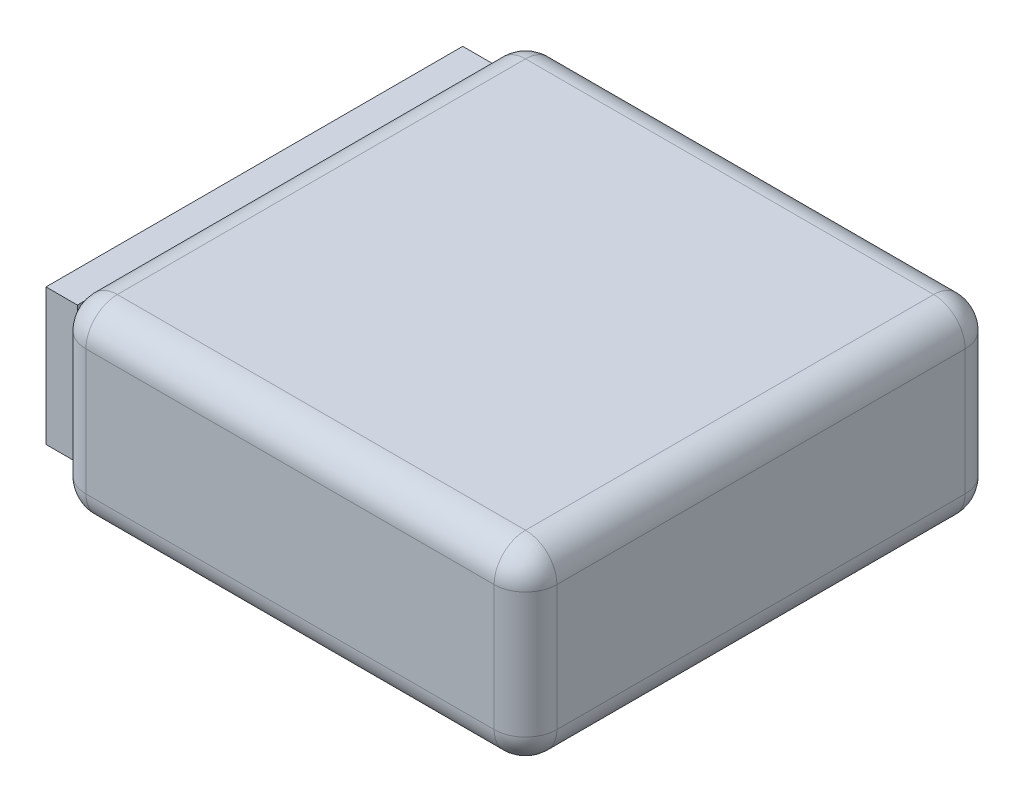
SolidWorks part; units mm, degrees
ref_plane "Front Plane" through (0, 0, 0) normal (0, 0, 1) x (1, 0, 0)
ref_plane "Top Plane" through (0, 0, 0) normal (0, 1, 0) x (1, 0, 0)
ref_plane "Right Plane" through (0, 0, 0) normal (1, 0, 0) x (0, 0, -1)
sketch "Sketch1" plane through (0, 0, 0) normal (0, 1, 0) x (1, 0, 0)
  line L1 (-19.787, -12.1518) -> (-4.787, -12.1518)
  line L2 (-19.787, -12.1518) -> (-19.787, 2.8482)
  line L3 (-19.787, 2.8482) -> (-4.787, 2.8482)
  line L4 (-4.787, -12.1518) -> (-4.787, 2.8482)
extrude "Boss-Extrude1" add sketch "Sketch1" along normal blind 6
fillet "Fillet1" radius 1 12 edges at (-19.787, 3, -2.8482) (-12.287, 0, -2.8482) (-19.787, 0, 4.6518) (-4.787, 0, 4.6518) (-12.287, 0, 12.1518) (-4.787, 3, -2.8482) (-4.787, 3, 12.1518) (-19.787, 3, 12.1518) (-19.787, 6, 4.6518) (-12.287, 6, -2.8482) (-4.787, 6, 4.6518) (-12.287, 6, 12.1518)
sketch "Sketch2" plane through (-19.787, 0, 0) normal (-1, 0, 0) x (0, 0, 1)
  line L1 (-1.8482, 1) -> (11.4238, 1)
  line L2 (-1.8482, 1) -> (-1.8482, 5.3462)
  line L3 (-1.8482, 5.3462) -> (11.4238, 5.3462)
  line L4 (11.4238, 1) -> (11.4238, 5.3462)
extrude "Boss-Extrude2" add sketch "Sketch2" along normal blind 1
